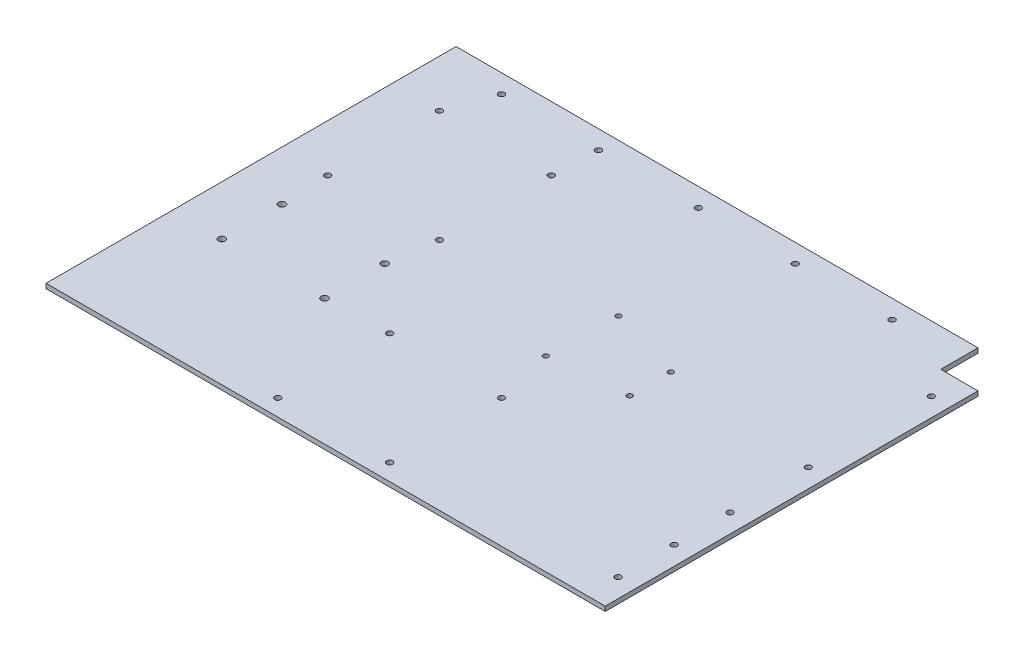
SolidWorks part; units mm, degrees
ref_plane "Front Plane" through (0, 0, 0) normal (0, 0, 1) x (1, 0, 0)
ref_plane "Top Plane" through (0, 0, 0) normal (0, 1, 0) x (1, 0, 0)
ref_plane "Right Plane" through (0, 0, 0) normal (1, 0, 0) x (0, 0, -1)
sketch "Sketch2" plane through (0, 0, 0) normal (0, 1, 0) x (1, 0, 0)
  line L1 (100.8006, -73.9205) -> (-280.1994, -73.9205)
  line L2 (100.8006, -73.9205) -> (100.8006, 180.0795)
  line L3 (75.4006, 205.4795) -> (-280.1994, 205.4795)
  line L4 (-280.1994, -73.9205) -> (-280.1994, 205.4795)
  line L5 (100.8006, -73.9205) -> (-280.1994, 205.4795) construction
  line L6 (75.4006, 19.8917) -> (-280.1994, -73.9205) construction
  line L7 (100.8006, 180.0795) -> (75.4006, 180.0795)
  line L10 (75.4006, 180.0795) -> (75.4006, 205.4795)
  point P0 (0, 0)
  dimension "D1" = 381
  dimension "D2" = 279.4
  dimension "D3" = 25.4
  dimension "D4" = 25.4
extrude "Boss-Extrude1" add sketch "Sketch2" along normal blind 3.175 contours L2 L7 L10 L3 L4 L1
sketch "Sketch3" plane through (0, 3.175, 0) normal (0, 1, 0) x (1, 0, 0)
  line L0 (100.8006, -73.9205) -> (100.8006, 30.0795) construction
  line L1 (100.8006, -73.9205) -> (100.8006, 180.0795) construction
  line L2 (100.8006, 30.0795) -> (-69.6283, 30.0795) construction
  line L3 (-69.6283, 30.0795) -> (-69.6283, -73.9205) construction
  line L4 (100.8006, -73.9205) -> (-280.1994, -73.9205) construction
  line L5 (-69.6283, -73.9205) -> (100.8006, -73.9205) construction
  line L6 (100.8006, -73.9205) -> (100.8006, 30.0795) construction
  line L7 (84.8006, 30.0795) -> (84.8006, -73.9205) construction
  dimension "D1" = 16
sketch "Sketch5" plane through (0, 3.175, 0) normal (0, 1, 0) x (1, 0, 0)
  line L0 (-280.1994, 192.7795) -> (75.4006, 192.7795) construction
  line L1 (-280.1994, -73.9205) -> (-280.1994, 205.4795) construction
  line L2 (75.4006, 180.0795) -> (75.4006, 205.4795) construction
  line L3 (75.4006, 205.4795) -> (-280.1994, 205.4795) construction
  circle A0 centre (-170.5048, 192.7795) radius 2.032
  circle A1 centre (-102.3994, 192.7795) radius 2.032
  circle A2 centre (-36.4852, 192.7795) radius 2.032
  circle A3 centre (-236.5448, 192.7795) radius 2.032
  circle A4 centre (29.5548, 192.7795) radius 2.032
  dimension "D2" = 4.064
  dimension "D3" = 4.064
  dimension "D4" = 4.064
  dimension "D5" = 134.0196
  dimension "D6" = 65.9142
  dimension "D9" = 66.04
  dimension "D1" = 12.7
  dimension "D7" = 2
  dimension "D8" = 2
extrude "Cut-Extrude2" cut sketch "Sketch5" against normal through all
sketch "Sketch6" plane through (0, 3.175, 0) normal (0, 1, 0) x (1, 0, 0)
  line L0 (88.1006, -73.9205) -> (88.1006, 180.0795) construction
  line L1 (-69.6283, -73.9205) -> (100.8006, -73.9205) construction
  line L2 (100.8006, 180.0795) -> (75.4006, 180.0795) construction
  line L3 (100.8006, -73.9205) -> (100.8006, 30.0795) construction
  circle A0 centre (88.1006, 161.0295) radius 2.032
  circle A1 centre (88.1006, 77.2095) radius 2.032
  circle A2 centre (88.1006, 23.8203) radius 2.032
  circle A3 centre (88.1006, -14.2797) radius 2.032
  circle A4 centre (88.1006, -52.3797) radius 2.032
  dimension "D2" = 4.064
  dimension "D3" = 4.064
  dimension "D4" = 19.05
  dimension "D5" = 83.82
  dimension "D6" = 4.064
  dimension "D7" = 53.3893
  dimension "D1" = 12.7
  dimension "D8" = 3
extrude "Cut-Extrude3" cut sketch "Sketch6" against normal through all
sketch "Sketch7" plane through (0, 3.175, 0) normal (0, 1, 0) x (1, 0, 0)
  line L0 (75.4006, 205.4795) -> (-280.1994, 205.4795) construction
  line L1 (100.8006, -73.9205) -> (100.8006, 180.0795) construction
  line L3 (-280.1994, -73.9205) -> (-280.1994, 205.4795) construction
  circle A0 centre (-14.9829, 86.5329) radius 1.778
  circle A1 centre (-14.9829, 58.5929) radius 1.778
  circle A2 centre (-67.0529, 53.5129) radius 1.778
  circle A3 centre (-65.7829, 101.7729) radius 1.778
  dimension "D1" = 3.556
  dimension "D2" = 3.556
  dimension "D3" = 3.556
  dimension "D4" = 3.556
  dimension "D11" = 118.9466
  dimension "D5" = 48.26
  dimension "D6" = 27.94
  dimension "D7" = 50.8
  dimension "D8" = 52.07
  dimension "D9" = 103.7066
  dimension "D10" = 166.5835
  dimension "D12" = 265.2165
extrude "Cut-Extrude4" cut sketch "Sketch7" against normal through all
sketch "Sketch8" plane through (0, 3.175, 0) normal (0, 1, 0) x (1, 0, 0)
  line L0 (-141.2479, -134.531) -> (-42.8328, -134.531) construction
sketch "Sketch10" plane through (0, 3.175, 0) normal (0, 1, 0) x (1, 0, 0)
  line L0 (75.4006, 205.4795) -> (-280.1994, 205.4795) construction
  circle A0 centre (-246.393, 53.0795) radius 2.3475
  circle A1 centre (-176.427, 53.0795) radius 2.3475
  circle A2 centre (-176.427, 12.0872) radius 2.3475
  circle A3 centre (-246.393, 12.0872) radius 2.3475
  dimension "D1" = 69.966
  dimension "D2" = 40.9923
  dimension "D4" = 40.9923
  dimension "D5" = 152.4
  dimension "D3" = 69.966
extrude "Cut-Extrude5" cut sketch "Sketch10" against normal through all
sketch "Sketch11" plane through (0, 3.175, 0) normal (0, 1, 0) x (1, 0, 0)
  circle A0 centre (-247.9076, 161.8493) radius 2.032
  circle A1 centre (-171.7076, 161.8493) radius 2.032
  circle A2 centre (-171.7076, 85.6493) radius 2.032
  circle A3 centre (-247.9076, 85.6493) radius 2.032
  circle A4 centre (-133.573, 13.6069) radius 2.032
  circle A5 centre (-57.373, 13.6069) radius 2.032
  circle A6 centre (-57.373, -62.5931) radius 2.032
  circle A7 centre (-133.573, -62.5931) radius 2.032
extrude "Cut-Extrude6" cut sketch "Sketch11" against normal through all
